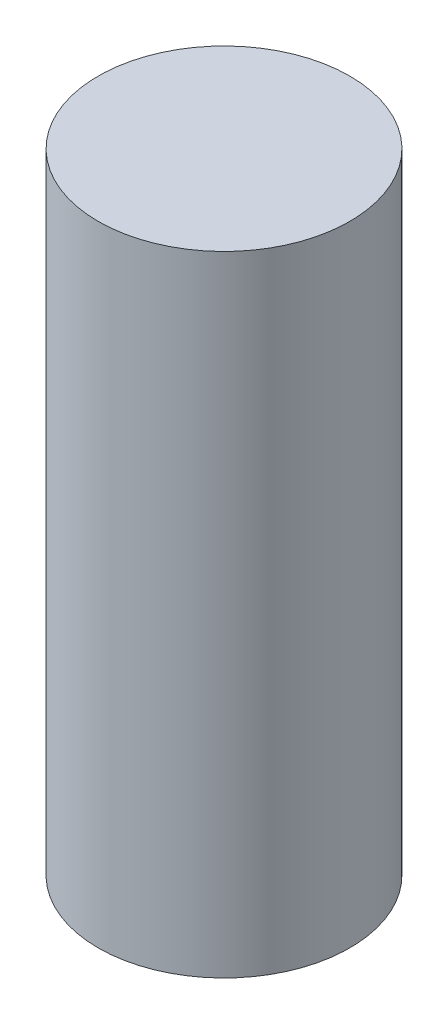
SolidWorks part; units mm, degrees
ref_plane "Front Plane" through (0, 0, 0) normal (0, 0, 1) x (1, 0, 0)
ref_plane "Top Plane" through (0, 0, 0) normal (0, 1, 0) x (1, 0, 0)
ref_plane "Right Plane" through (0, 0, 0) normal (1, 0, 0) x (0, 0, -1)
sketch "Sketch1" plane through (0, 0, 0) normal (0, 1, 0) x (1, 0, 0)
  circle A0 centre (0, 0) radius 5
  dimension "D1" = 10
extrude "Boss-Extrude1" add sketch "Sketch1" along normal blind 25
